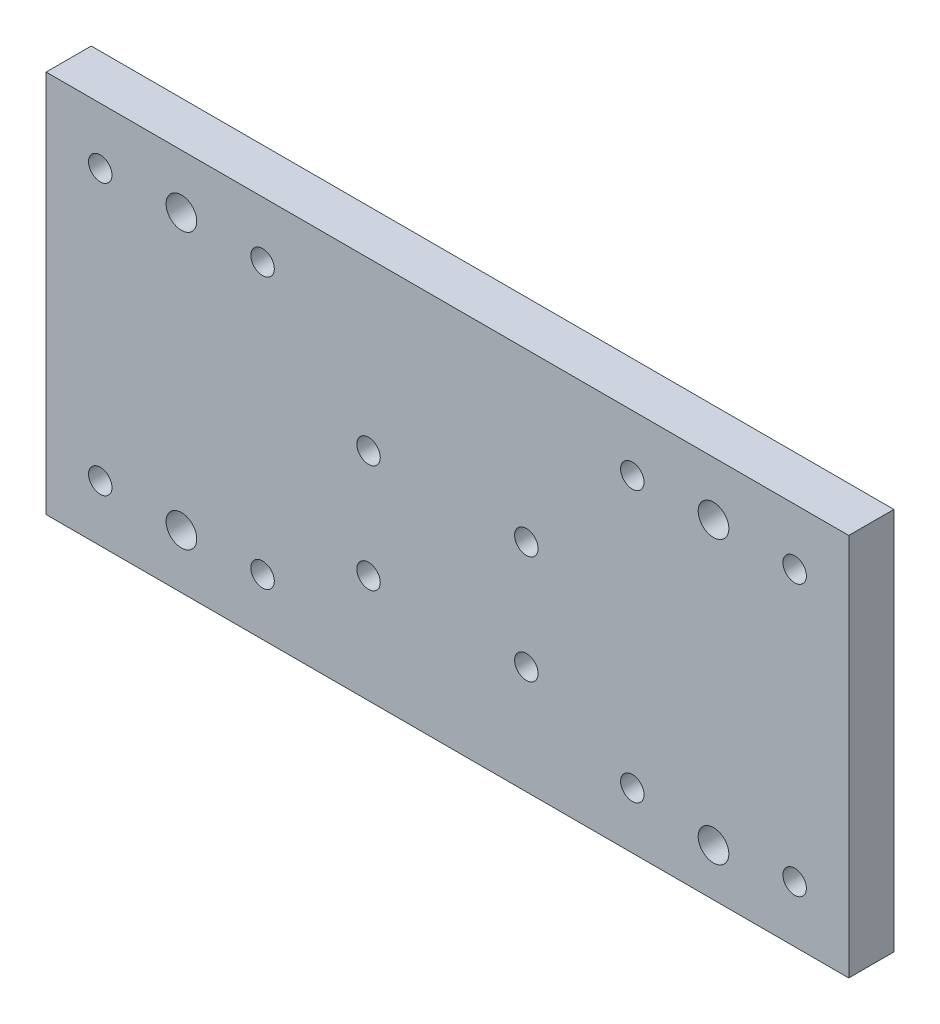
SolidWorks part; units mm, degrees
ref_plane "Front Plane" through (0, 0, 0) normal (0, 0, 1) x (1, 0, 0)
ref_plane "Top Plane" through (0, 0, 0) normal (0, 1, 0) x (1, 0, 0)
ref_plane "Right Plane" through (0, 0, 0) normal (1, 0, 0) x (0, 0, -1)
sketch "Sketch1" plane through (0, 0, 0) normal (0, 0, 1) x (1, 0, 0)
  line L1 (-89, 42.5) -> (89, 42.5)
  line L3 (-89, -42.5) -> (89, -42.5)
  line L5 (-89, 42.5) -> (89, -42.5) construction
  line L6 (-89, -42.5) -> (89, 42.5) construction
  line L9 (-89, 42.5) -> (-89, -42.5)
  line L10 (0, 42.5) -> (0, -42.5) construction
  line L14 (89, 42.5) -> (89, -42.5)
  line L15 (-59, 42.5) -> (-59, -42.5) construction
  line L16 (-100, 0) -> (90.963, 0) construction
  line L17 (-89, -6.5) -> (89, -6.5) construction
  circle A0 centre (-77, -30) radius 2.6
  circle A1 centre (-41, -30) radius 2.6
  circle A2 centre (-41, 30) radius 2.6
  circle A3 centre (-77, 30) radius 2.6
  circle A4 centre (-17.5, -18.5) radius 2.6
  circle A5 centre (17.5, -18.5) radius 2.6
  circle A6 centre (17.5, 5.5) radius 2.6
  circle A7 centre (-17.5, 5.5) radius 2.6
  circle A8 centre (77, -30) radius 2.6
  circle A9 centre (41, -30) radius 2.6
  circle A10 centre (41, 30) radius 2.6
  circle A11 centre (77, 30) radius 2.6
  point P0 (0, 0)
  dimension "D6" = 5.2
  dimension "D9" = 5.2
  dimension "D3" = 24
  dimension "D12" = 36
  dimension "D13" = 60
  dimension "D1" = 178
  dimension "D2" = 85
  dimension "D4" = 36
  dimension "D5" = 59
  dimension "D7" = 2
  dimension "D8" = 2
  dimension "D10" = 2
  dimension "D11" = 2
extrude "Boss-Extrude1" add sketch "Sketch1" along normal blind 10
hole_wizard "M8 Tapped Hole1" positions "Sketch4" profile "Sketch5" tap size "M8" standard "ISO" end condition through all
sketch "Sketch4" plane through (0, 0, 10) normal (0, 0, 1) x (1, 0, 0)
  line L0 (0, 42.5) -> (0, -42.5) construction
  line L1 (89, 42.5) -> (-89, 42.5) construction
  line L2 (-89, -42.5) -> (89, -42.5) construction
  line L3 (-89, 0) -> (89, 0) construction
  line L4 (-89, 42.5) -> (-89, -42.5) construction
  line L5 (89, -42.5) -> (89, 42.5) construction
  point P7 (-59, 30.5)
  point P9 (-59, -30.5)
  point P16 (59, -32)
  point P17 (59, 30.5)
  point P52 (0, 0)
  point P53 (59, -16.7754)
  point P54 (59, -37.6843)
  dimension "D1" = 61
  dimension "D2" = 59
  dimension "D3" = 1.5
sketch "Sketch5" plane through (59, 30.5, 10) normal (1, 0, 0) x (0, -1, 0)
  line L0 (0, 0) -> (0, 10)
  line L1 (0, 10) -> (3.4, 10)
  line L2 (3.4, 10) -> (3.4, 0)
  line L5 (3.4, 0) -> (0, 0)
  line L11 (0, -6.35) -> (0, 107.95) construction
  dimension "Thru Tap Drill Dia." = 6.8
  dimension "Thru Tap Drill Depth" = 10
cosmetic thread "Hole Thread5" parameters "D2"=8
cosmetic thread "Hole Thread6" parameters "D2"=8
cosmetic thread "Hole Thread7" parameters "D2"=8
cosmetic thread "Hole Thread8" parameters "D2"=8
equation "\"149、2\"=59"
